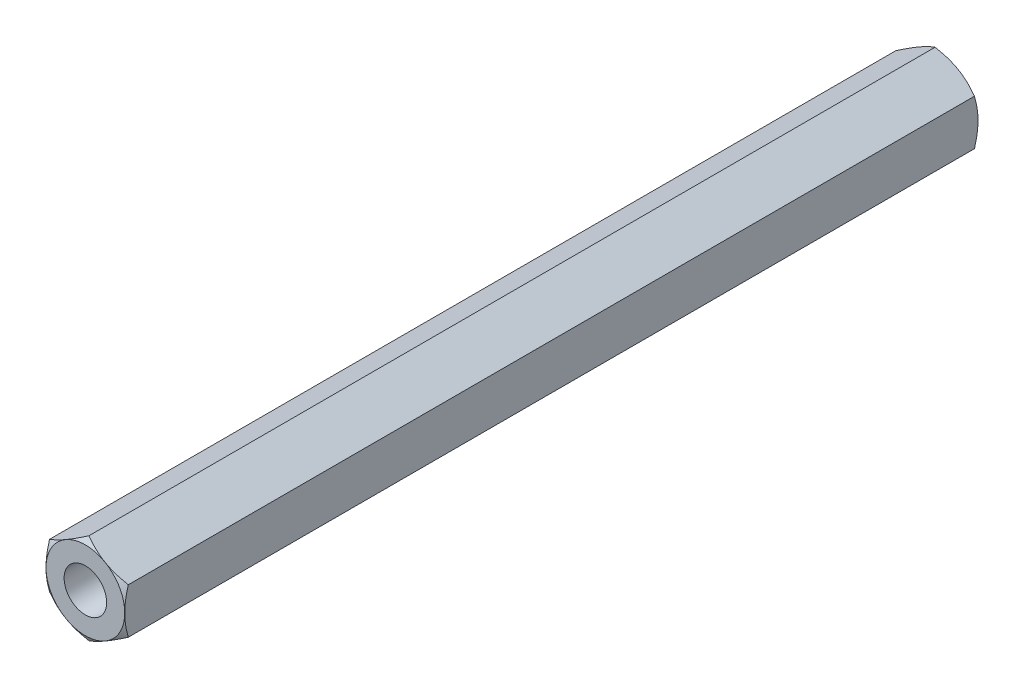
SolidWorks part; units mm, degrees
ref_plane "基准面1" through (0, 0, 0) normal (0, 0, 1) x (1, 0, 0)
ref_plane "基准面2" through (0, 0, 0) normal (0, 1, 0) x (1, 0, 0)
ref_plane "基准面3" through (0, 0, 0) normal (1, 0, 0) x (0, 0, -1)
sketch "尺寸草图" plane through (0, 0, 0) normal (0, 0, 1) x (1, 0, 0)
  line L0 (0, 0) -> (7.7, 0) construction
  line L1 (0, 0) -> (15.4, 0) construction
  line L2 (7.7, 0) -> (13.6, 0) construction
  line L3 (-3.8095, 0) -> (0, 0) construction
  point P3 (4, 0)
  point P4 (0.7, 0)
  point P5 (7.7, 0)
  point P6 (3.2, 0)
  point P8 (7, 0)
  dimension "D1" = 3.8095
  dimension "D" = 4
  dimension "P" = 0.7
  dimension "e(最小)" = 7.7
  dimension "m(最大)" = 3.2
  dimension "s(公称)" = 7
  dimension "dw(最小)" = 5.9
sketch "草图1" plane through (0, 0, 0) normal (0, 0, 1) x (1, 0, 0)
  line L0 (-3, 0) -> (3, 0) construction
  line L1 (0, 3.4641) -> (0, -3.4641) construction
  line L3 (0, 3.4641) -> (-3, 1.7321)
  line L4 (-3, 1.7321) -> (-3, -1.7321)
  line L5 (-3, -1.7321) -> (0, -3.4641)
  line L6 (0, -3.4641) -> (3, -1.7321)
  line L7 (3, -1.7321) -> (3, 1.7321)
  line L8 (3, 1.7321) -> (0, 3.4641)
  circle A0 centre (0, 0) radius 3 construction
  circle A1 centre (0, 0) radius 1.6211
  point P2 (0, 3.4859)
  dimension "D1" = 6.95
  dimension "D" = 3.2422
  dimension "D2" = 6
extrude "基体-拉伸" add sketch "草图1" along normal blind 65
cosmetic thread "装饰螺纹线1" parameters "D2"=4
sketch "草图2" plane through (0, 0, 0) normal (0, 0, -1) x (-1, 0, 0)
  circle A0 centre (0, 0) radius 3
  circle A1 centre (0, 0) radius 1.6211 construction
  dimension "s" = 6
extrude "切除-拉伸1" cut sketch "草图2" against normal through all draft 60 flip side to cut
sketch "草图3" plane through (0, 0, 65) normal (0, 0, 1) x (1, 0, 0)
  circle A0 centre (0, 0) radius 3
  dimension "D1" = 6
extrude "切除-拉伸2" cut sketch "草图3" against normal through all draft 60 flip side to cut
